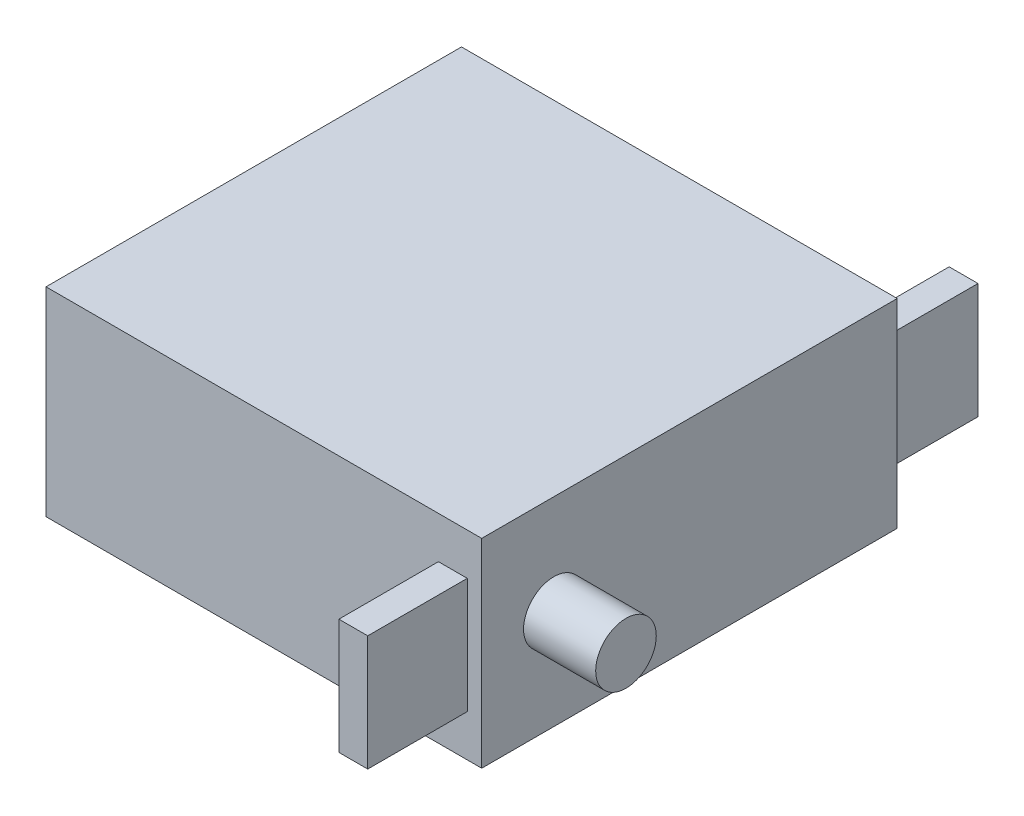
SolidWorks part; units mm, degrees
ref_plane "Front Plane" through (0, 0, 0) normal (0, 0, 1) x (1, 0, 0)
ref_plane "Top Plane" through (0, 0, 0) normal (0, 1, 0) x (1, 0, 0)
ref_plane "Right Plane" through (0, 0, 0) normal (1, 0, 0) x (0, 0, -1)
sketch "Sketch1" plane through (0, 0, 0) normal (0, 1, 0) x (1, 0, 0)
  line L1 (0, 0) -> (30.2, 0)
  line L2 (0, 0) -> (0, 28.8)
  line L3 (0, 28.8) -> (30.2, 28.8)
  line L4 (30.2, 0) -> (30.2, 28.8)
  dimension "D1" = 28.8
  dimension "D2" = 30.2
extrude "Boss-Extrude1" add sketch "Sketch1" along normal mid plane 13.8
sketch "Sketch2" plane through (30.2, 0, 0) normal (1, 0, 0) x (0, 0, -1)
  line L0 (0, 6.9) -> (0, -6.9) construction
  circle A0 centre (5, 0) radius 2.1
  dimension "D1" = 4.2
  dimension "D2" = 5
extrude "Boss-Extrude2" add sketch "Sketch2" along normal blind 5
sketch "Sketch3" plane through (0, 0, 0) normal (0, 0, 1) x (1, 0, 0)
  line L0 (30.2, 6.9) -> (30.2, -6.9) construction
  line L1 (27.2, 4) -> (29.2, 4)
  line L2 (27.2, 4) -> (27.2, -4)
  line L3 (27.2, -4) -> (29.2, -4)
  line L4 (29.2, 4) -> (29.2, -4)
  point P6 (30.2, 0)
  point P7 (29.2, 0)
  dimension "D1" = 8
  dimension "D2" = 2
  dimension "D3" = 1
extrude "Boss-Extrude3" add sketch "Sketch3" along normal blind 6.9
sketch "Sketch4" plane through (0, 0, -28.8) normal (0, 0, -1) x (-1, 0, 0)
  line L4 (-27.2, -4) -> (-27.2, 4)
  line L5 (-29.2, -4) -> (-27.2, -4)
  line L6 (-29.2, 4) -> (-29.2, -4)
  line L7 (-27.2, 4) -> (-29.2, 4)
  line L8 (-27.2, -4) -> (-27.2, 4)
  line L9 (-29.2, -4) -> (-27.2, -4)
  line L10 (-29.2, 4) -> (-29.2, -4)
  line L11 (-27.2, 4) -> (-29.2, 4)
  dimension "D1" = 0
extrude "Boss-Extrude4" add sketch "Sketch4" along normal blind 6.6
equation "\"D1@Boss-Extrude3\"=(42-28.2)/2"
equation "\"D1@Boss-Extrude4\"=(42-28.8)/2"
